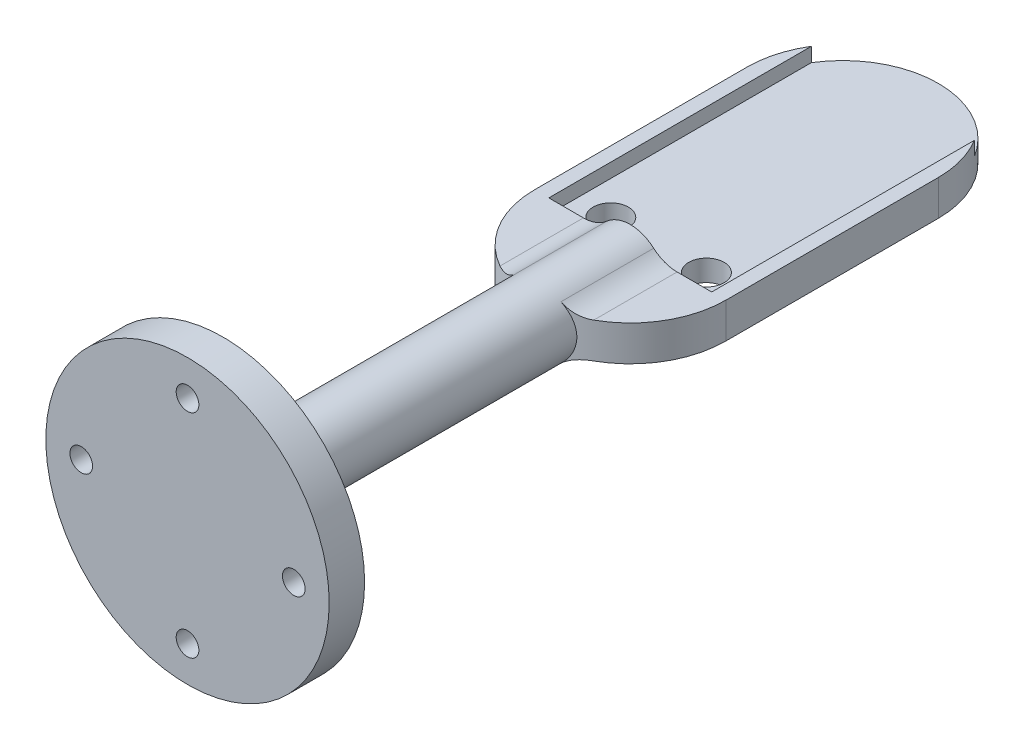
SolidWorks part; units mm, degrees
ref_plane "前视基准面" through (0, 0, 0) normal (0, 0, 1) x (1, 0, 0)
ref_plane "上视基准面" through (0, 0, 0) normal (0, 1, 0) x (1, 0, 0)
ref_plane "右视基准面" through (0, 0, 0) normal (1, 0, 0) x (0, 0, -1)
other "Configuration Table"
sketch "草图1" plane through (0, 0, 0) normal (0, 0, 1) x (1, 0, 0)
  circle A0 centre (0, 0) radius 15 construction
  circle A1 centre (0, 15) radius 1.6
  circle A2 centre (15, 0) radius 1.6
  circle A3 centre (0, -15) radius 1.6
  circle A4 centre (-15, 0) radius 1.6
  circle A5 centre (0, 0) radius 20
  point P14 (0, 0)
  dimension "D1" = 30
  dimension "D2" = 3.2
  dimension "D4" = 40
  dimension "D3" = 4
extrude "凸台-拉伸1" add sketch "草图1" along normal mid plane 5
sketch "草图4" plane through (0, 0, 0) normal (0, 1, 0) x (1, 0, 0)
  line L0 (0, 0) -> (0, 60)
  dimension "D1" = 60
sweep "扫描1" add path "草图4" circular profile diameter 10 parameters "D3"=10
sketch "草图9" plane through (0, 0, 0) normal (0, 1, 0) x (1, 0, 0)
  line L0 (0, 90) -> (0, 60) construction
  line L1 (5, 60) -> (-5, 60) construction
  line L2 (13.5, 90) -> (13.5, 60)
  line L3 (-13.5, 90) -> (-13.5, 60)
  arc A0 (13.5, 90) -> (-13.5, 90) centre (0, 90) ccw
  arc A1 (-13.5, 60) -> (13.5, 60) centre (0, 60) ccw
  point P4 (0, 75)
  dimension "D1" = 27
  dimension "D2" = 30
extrude "凸台-拉伸2" add sketch "草图9" along normal mid plane 5
sketch "草图10" plane through (0, 2.5, 0) normal (0, 1, 0) x (1, 0, 0)
  line L0 (0, -1000) -> (0, 49000) construction
  line L1 (4.3301, 60) -> (-4.3301, 60) construction
  line L2 (-11.5, 104.6508) -> (11.5, 104.6508)
  line L3 (-11.5, 104.6508) -> (-11.5, 60)
  line L4 (-11.5, 60) -> (11.5, 60)
  line L5 (11.5, 104.6508) -> (11.5, 60)
  line L6 (-11.5, 104.6508) -> (11.5, 60) construction
  line L7 (-11.5, 60) -> (11.5, 104.6508) construction
  point P1 (0, 82.3254)
  dimension "D1" = 23
extrude "切除-拉伸1" cut sketch "草图10" against normal blind 2
sketch "草图11" plane through (0, 0.5, 0) normal (0, 1, 0) x (1, 0, 0)
  line L0 (0, -1000) -> (0, 49000) construction
  line L1 (-11.5, 60) -> (11.5, 60) construction
  circle A0 centre (-6.75, 64) radius 2.5
  circle A1 centre (6.75, 64) radius 2.5
  dimension "D1" = 5
  dimension "D2" = 13.5
  dimension "D3" = 4
extrude "切除-拉伸2" cut sketch "草图11" against normal through all
fillet "圆角1" radius 5 5 edges at (5, 0, -2.5) (4.3301, 2.5, -53.6066) (-4.3301, 2.5, -53.6066) (-4.3301, -2.5, -53.6066) (4.3301, -2.5, -53.6066)
